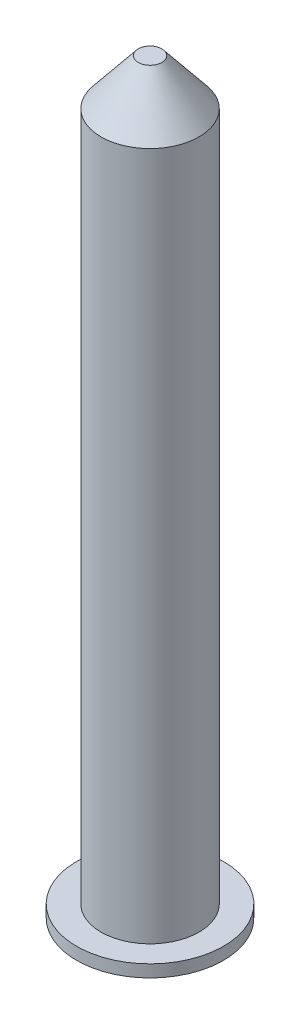
SolidWorks part; units mm, degrees
ref_plane "Front Plane" through (0, 0, 0) normal (0, 0, 1) x (1, 0, 0)
ref_plane "Top Plane" through (0, 0, 0) normal (0, 1, 0) x (1, 0, 0)
ref_plane "Right Plane" through (0, 0, 0) normal (1, 0, 0) x (0, 0, -1)
sketch "Sketch2" plane through (0, 0, 0) normal (0, 1, 0) x (1, 0, 0)
  circle A0 centre (0, 0) radius 2.54
extrude "Boss-Extrude1" add sketch "Sketch2" along normal blind 38.1
chamfer "Chamfer1" distance 2.38 angle 39 1 edges at (0, 38.1, 2.54)
sketch "Sketch3" plane through (0, 0, 0) normal (0, -1, 0) x (-1, 0, 0)
  circle A0 centre (0, 0) radius 3.81
extrude "Boss-Extrude2" add sketch "Sketch3" along normal blind 0.635
